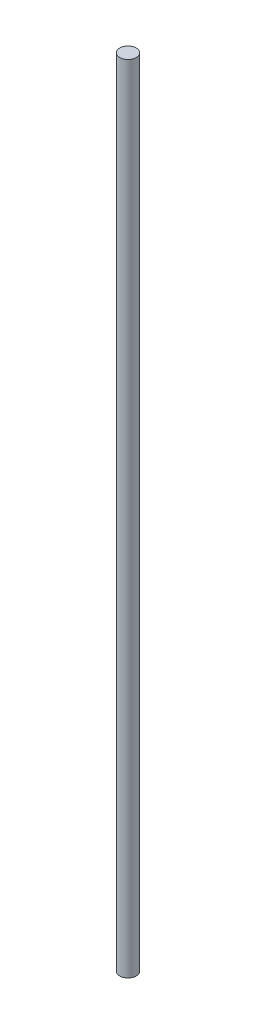
SolidWorks part; units mm, degrees
ref_plane "Front" through (0, 0, 0) normal (0, 0, 1) x (1, 0, 0)
ref_plane "Top" through (0, 0, 0) normal (0, 1, 0) x (1, 0, 0)
ref_plane "Right" through (0, 0, 0) normal (1, 0, 0) x (0, 0, -1)
sketch "Sketch1" plane through (0, 0, 0) normal (0, 1, 0) x (1, 0, 0)
  circle A0 centre (0, 0) radius 4
  dimension "D1" = 8
extrude "Boss-Extrude1" add sketch "Sketch1" along normal blind 385
